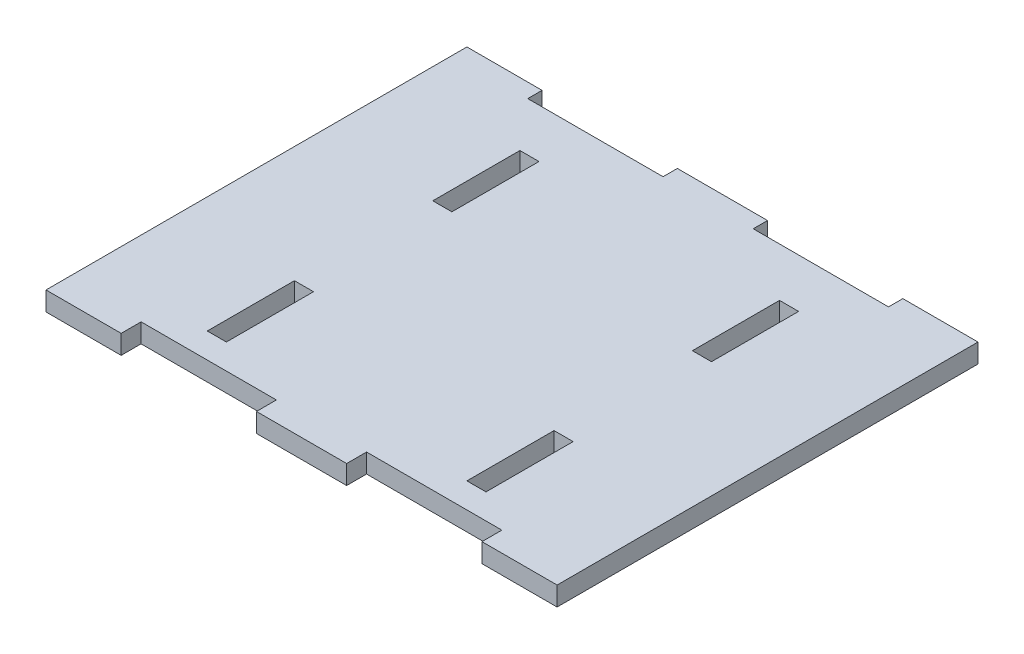
SolidWorks part; units mm, degrees
ref_plane "Front Plane" through (0, 0, 0) normal (0, 0, 1) x (1, 0, 0)
ref_plane "Top Plane" through (0, 0, 0) normal (0, 1, 0) x (1, 0, 0)
ref_plane "Right Plane" through (0, 0, 0) normal (1, 0, 0) x (0, 0, -1)
sketch "Sketch1" plane through (0, 0, 0) normal (0, 1, 0) x (1, 0, 0)
  line L1 (0, 0) -> (85, 0)
  line L2 (0, 0) -> (0, 70)
  line L3 (0, 70) -> (85, 70)
  line L4 (85, 0) -> (85, 70)
  dimension "D1" = 85
  dimension "D2" = 70
extrude "Boss-Extrude1" add sketch "Sketch1" along normal blind 3.175
sketch "Sketch2" plane through (0, 0, 0) normal (0, -1, 0) x (1, 0, 0)
  line L0 (0, 0) -> (85, 0) construction
  line L1 (19.325, -7.5) -> (22.5, -7.5)
  line L2 (19.325, -7.5) -> (19.325, -21.992)
  line L3 (19.325, -21.992) -> (22.5, -21.992)
  line L4 (22.5, -7.5) -> (22.5, -21.992)
  line L5 (19.325, -45) -> (22.5, -45)
  line L6 (19.325, -45) -> (19.325, -59.492)
  line L7 (19.325, -59.492) -> (22.5, -59.492)
  line L8 (22.5, -45) -> (22.5, -59.492)
  line L9 (62.5, -7.5) -> (65.675, -7.5)
  line L10 (62.5, -7.5) -> (62.5, -21.992)
  line L11 (62.5, -21.992) -> (65.675, -21.992)
  line L12 (65.675, -7.5) -> (65.675, -21.992)
  line L13 (62.5, -45) -> (65.675, -45)
  line L14 (62.5, -45) -> (62.5, -59.492)
  line L15 (62.5, -59.492) -> (65.675, -59.492)
  line L16 (65.675, -45) -> (65.675, -59.492)
  line L17 (85, -70) -> (0, -70) construction
  line L18 (50, -70) -> (72.5, -70)
  line L19 (50, -70) -> (50, -67.6188)
  line L20 (50, -67.6188) -> (72.5, -67.6188)
  line L21 (72.5, -70) -> (72.5, -67.6188)
  line L22 (85, 0) -> (85, -70) construction
  line L23 (35, -70) -> (12.5, -70)
  line L24 (35, -70) -> (35, -67.6188)
  line L25 (35, -67.6188) -> (12.5, -67.6188)
  line L26 (12.5, -70) -> (12.5, -67.6188)
  line L27 (0, -70) -> (0, 0) construction
  line L29 (72.5, -3.313) -> (50, -3.313)
  line L30 (72.5, -3.313) -> (72.5, 0)
  line L31 (72.5, 0) -> (50, 0)
  line L32 (50, -3.313) -> (50, 0)
  line L33 (35, -3.313) -> (12.5, -3.313)
  line L34 (35, -3.313) -> (35, 0)
  line L35 (35, 0) -> (12.5, 0)
  line L36 (12.5, -3.313) -> (12.5, 0)
  point P30 (50, -68.8094)
  dimension "D1" = 14.492
  dimension "D2" = 14.492
  dimension "D3" = 23.008
  dimension "D4" = 7.5
  dimension "D5" = 2.3813
  dimension "D6" = 12.5
  dimension "D7" = 15
  dimension "D8" = 22.5
  dimension "D9" = 12.5
  dimension "D10" = 12.5
  dimension "D11" = 22.5
  dimension "D12" = 15
  dimension "D13" = 22.5
  dimension "D14" = 3.313
extrude "Cut-Extrude1" cut sketch "Sketch2" against normal through all
